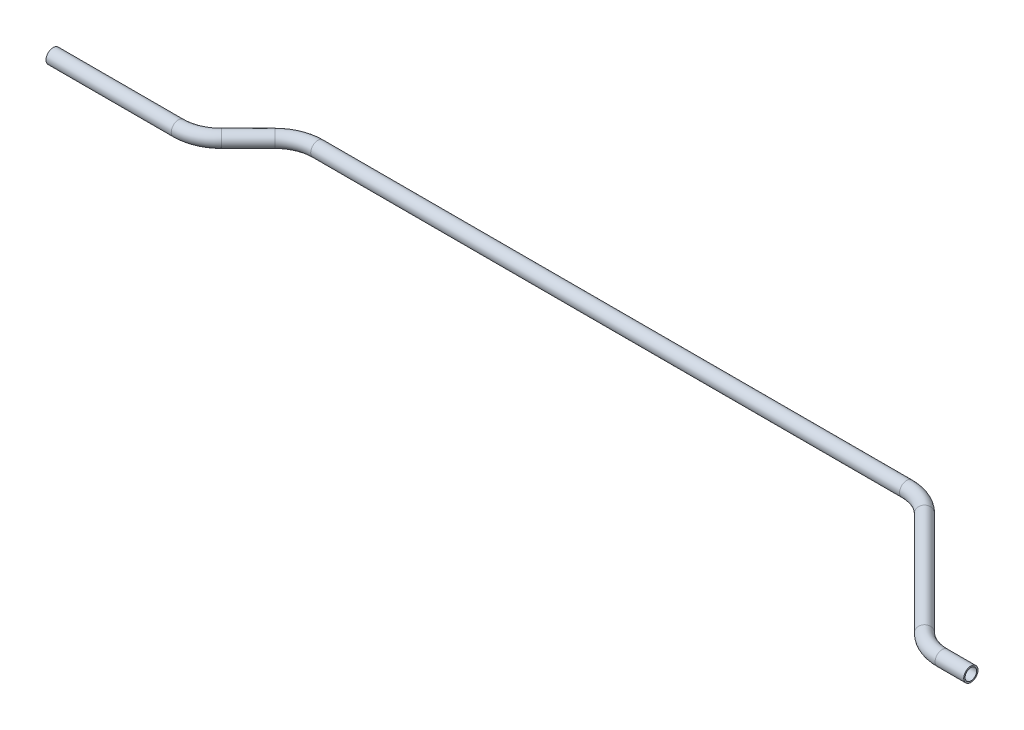
SolidWorks part; units mm, degrees
material "AISI Type 316L stainless steel"
ref_plane "Front Plane" through (0, 0, 0) normal (0, 0, 1) x (1, 0, 0)
ref_plane "Top Plane" through (0, 0, 0) normal (0, 1, 0) x (1, 0, 0)
ref_plane "Right Plane" through (0, 0, 0) normal (1, 0, 0) x (0, 0, -1)
sketch "Sketch1" plane through (0, 0, 0) normal (0, 1, 0) x (1, 0, 0)
  line L0 (0, 0) -> (111.2185, 0)
  line L1 (138.1592, 11.1592) -> (161.9846, 34.9846)
  line L2 (188.9254, 46.1439) -> (711.8133, 46.1439)
  line L3 (738.7541, 34.9846) -> (830.7356, -56.9969)
  line L4 (857.6764, -68.1561) -> (883.0764, -68.1561)
  arc A0 (830.7356, -56.9969) -> (857.6764, -68.1561) centre (857.6764, -30.0561) ccw
  arc A1 (711.8133, 46.1439) -> (738.7541, 34.9846) centre (711.8133, 8.0439) cw
  arc A2 (161.9846, 34.9846) -> (188.9254, 46.1439) centre (188.9254, 8.0439) cw
  arc A3 (111.2185, 0) -> (138.1592, 11.1592) centre (111.2185, 38.1) ccw
  point P9 (841.8949, -68.1561)
  point P12 (727.5949, 46.1439)
  point P15 (173.1439, 46.1439)
  point P18 (127, 0)
  dimension "D8" = 38.1
  dimension "D1" = 127
  dimension "D2" = 135
  dimension "D3" = 25.4
  dimension "D4" = 883.0764
  dimension "D5" = 114.3
  dimension "D6" = 45
  dimension "D7" = 46.1439
ref_plane "Plane1" through (0, 0, 0) normal (1, 0, 0) x (0, 0, -1)
sketch "Sketch2" plane through (0, 0, 0) normal (1, 0, 0) x (0, 0, -1)
  circle A0 centre (0, 0) radius 6.35
  circle A1 centre (0, 0) radius 5.1054
  dimension "D1" = 12.7
  dimension "D2" = 1.2446
sweep "Sweep1" add profiles "Sketch2" path "Sketch1"
